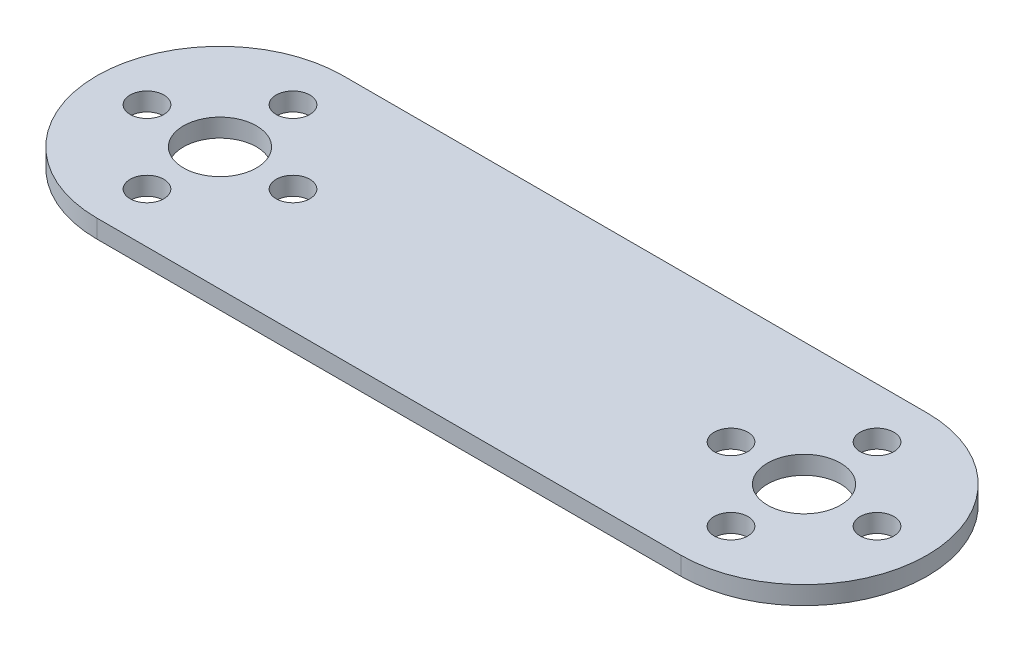
SolidWorks part; units mm, degrees
material "2024 Alloy"
ref_plane "Front Plane" through (0, 0, 0) normal (0, 0, 1) x (1, 0, 0)
ref_plane "Top Plane" through (0, 0, 0) normal (0, 1, 0) x (1, 0, 0)
ref_plane "Right Plane" through (0, 0, 0) normal (1, 0, 0) x (0, 0, -1)
ref_plane "Plane1" through (0, 2, 0) normal (0, 1, 0) x (1, 0, 0)
sketch "Sketch1" plane through (0, 2, 0) normal (0, 1, 0) x (1, 0, 0)
  line L0 (64, 13.5) -> (0, 13.5)
  line L1 (0, -13.5) -> (64, -13.5)
  circle A0 centre (56, 0) radius 1.85
  circle A1 centre (64, -8) radius 1.85
  circle A2 centre (72, 0) radius 1.85
  circle A3 centre (64, 8) radius 1.85
  circle A4 centre (64, 0) radius 4
  circle A5 centre (-8, 0) radius 1.85
  circle A6 centre (0, -8) radius 1.85
  circle A7 centre (8, 0) radius 1.85
  circle A8 centre (0, 8) radius 1.85
  circle A9 centre (0, 0) radius 4
  arc A10 (0, 13.5) -> (0, -13.5) centre (0, 0) ccw
  arc A11 (64, -13.5) -> (64, 13.5) centre (64, 0) ccw
extrude "Boss-Extrude1" add sketch "Sketch1" against normal blind 2
